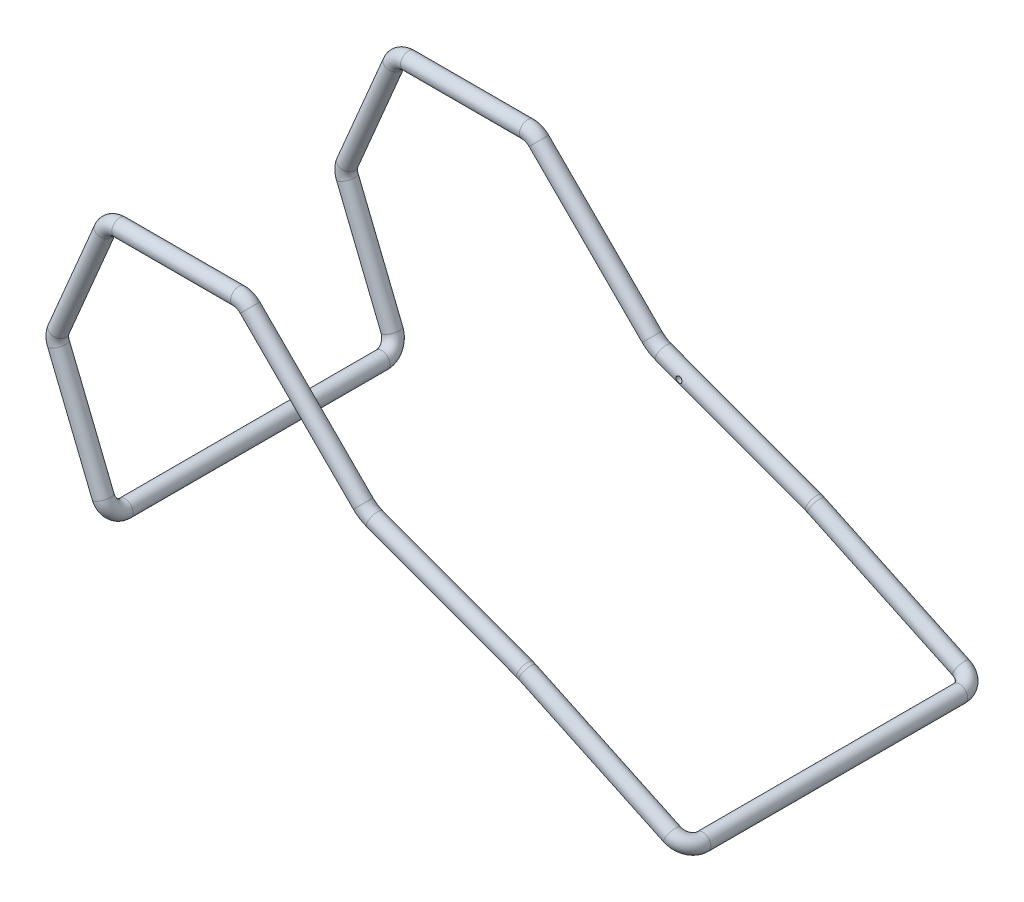
SolidWorks part; units mm, degrees
ref_plane "Front Plane" through (0, 0, 0) normal (0, 0, 1) x (1, 0, 0)
ref_plane "Top Plane" through (0, 0, 0) normal (0, 1, 0) x (1, 0, 0)
ref_plane "Right Plane" through (0, 0, 0) normal (1, 0, 0) x (0, 0, -1)
ref_plane "Plane1" through (0, 0, 304.8) normal (0, 0, 1) x (1, 0, 0)
ref_plane "Plane2" through (0, 0, -25.4) normal (0, 0, 1) x (1, 0, 0)
sketch3d "3DSketch1"
  line L0 (-9.5303, 23.5443, 0) -> (-80.1831, 198.0889, 0)
  line L1 (-80.0261, 217.5286, 0) -> (-6.5635, 390.9094, 0)
  line L2 (16.8238, 406.4, 0) -> (205.1258, 406.4, 0)
  line L3 (223.0863, 398.9605, 0) -> (402.1917, 219.8551, 0)
  line L4 (420.5449, 208.1105, 0) -> (658.2098, 120.5156, 0)
  line L5 (662.2973, 118.8031, 0) -> (891.4235, 10.8277, 0)
  line L6 (205.1258, 424.1672, 0) -> (205.1258, 377.3241, 0) construction
  line L8 (891.4235, 10.8277, -457.2) -> (662.2973, 118.8031, -457.2)
  line L11 (205.1258, 406.4, -457.2) -> (16.8238, 406.4, -457.2)
  line L12 (-6.5635, 390.9094, -457.2) -> (-80.0261, 217.5286, -457.2)
  line L13 (-80.1831, 198.0889, -457.2) -> (-9.5303, 23.5443, -457.2)
  line L15 (-6.5635, 390.9094, 0) -> (-6.5635, 390.9094, -457.2) construction
  line L16 (205.1258, 406.4, 0) -> (205.1258, 406.4, -457.2) construction
  line L17 (402.1917, 219.8551, 0) -> (402.1917, 219.8551, -457.2) construction
  line L18 (658.2098, 120.5156, 0) -> (658.2098, 120.5156, -457.2) construction
  line L19 (658.2098, 120.5156, -457.2) -> (420.5449, 208.1105, -457.2)
  line L20 (402.1917, 219.8551, -457.2) -> (223.0863, 398.9605, -457.2)
  line L21 (-6.5635, 390.9094, 0) -> (0, 406.4, 0) construction
  line L22 (0, 406.4, 0) -> (16.8238, 406.4, 0) construction
  line L23 (914.4, 0, -25.4) -> (914.4, 0, -431.8)
  line L24 (0, 0, -431.8) -> (0, 0, -25.4)
  line L25 (0, 0, -25.4) -> (0, 0, 0) construction
  line L26 (0, 0, -25.4) -> (914.4, 0, -25.4) construction
  line L27 (914.4, 0, -431.8) -> (0, 0, -431.8) construction
  arc A0 (-6.5635, 390.9094, 0) -> (16.8238, 406.4, 0) centre (16.8238, 381, 0) cw
  arc A1 (-80.0261, 217.5286, 0) -> (-80.1831, 198.0889, 0) centre (-56.6388, 207.6192, 0) cw
  arc A2 (205.1258, 406.4, 0) -> (223.0863, 398.9605, 0) centre (205.1258, 381, 0) cw
  arc A3 (402.1917, 219.8551, 0) -> (420.5449, 208.1105, 0) centre (438.1127, 255.7761, 0) cw
  arc A4 (658.2098, 120.5156, 0) -> (662.2973, 118.8031, 0) centre (640.642, 72.85, 0) cw
  arc A5 (891.4235, 10.8277, 0) -> (914.4, 0, -25.4) centre (891.4235, 10.8277, -25.4) ccw
  arc A6 (-80.0261, 217.5286, -457.2) -> (-80.1831, 198.0889, -457.2) centre (-56.6388, 207.6192, -457.2) ccw
  arc A7 (223.0863, 398.9605, -457.2) -> (205.1258, 406.4, -457.2) centre (205.1258, 381, -457.2) ccw
  arc A8 (16.8238, 406.4, -457.2) -> (-6.5635, 390.9094, -457.2) centre (16.8238, 381, -457.2) ccw
  arc A9 (662.2973, 118.8031, -457.2) -> (658.2098, 120.5156, -457.2) centre (640.642, 72.85, -457.2) ccw
  arc A10 (402.1917, 219.8551, -457.2) -> (420.5449, 208.1105, -457.2) centre (438.1127, 255.7761, -457.2) ccw
  arc A11 (914.4, 0, -431.8) -> (891.4235, 10.8277, -457.2) centre (891.4235, 10.8277, -431.8) ccw
  arc A12 (-9.5303, 23.5443, 0) -> (0, 0, -25.4) centre (-9.5303, 23.5443, -25.4) ccw
  arc A13 (-9.5303, 23.5443, -457.2) -> (0, 0, -431.8) centre (-9.5303, 23.5443, -431.8) ccw
  point P5 (892.403, 12.7, 0)
  point P7 (902.2511, 33.8042, -25.4)
  point P18 (16.8238, 381, -25.4)
  point P22 (-56.6388, 207.6192, 25.4)
  point P26 (205.1258, 381, -25.4)
  point P30 (438.1127, 255.7761, 50.8)
  point P34 (640.642, 72.85, -50.8)
  point P39 (-56.6388, 207.6192, -431.8)
  point P43 (0, 0, 0)
  point P44 (205.1258, 381, -431.8)
  point P48 (902.2511, 33.8042, -431.8)
  point P49 (16.8238, 381, -431.8)
  point P52 (660.2909, 119.7486, -457.2)
  point P53 (640.642, 72.85, -406.4)
  point P57 (438.1127, 255.7761, -406.4)
  point P59 (0, 0, 0)
  point P60 (14.0139, 33.0746, -25.4)
  point P64 (-33.0746, 14.0139, -431.8)
  point P65 (0, 0, 0)
  point P67 (469.8666, 237.3101, 0)
  point P68 (0, 0, 0)
  point P69 (0, 0, 0)
  dimension "D8" = 25.4
  dimension "D9" = 50.8
  dimension "D6" = 25.4
  dimension "D11" = 50.8
  dimension "D12" = 25.4
  dimension "D1" = 175
  dimension "D2" = 914.4
  dimension "D4" = 135
  dimension "D5" = 406.4
  dimension "D7" = 457.2
  dimension "D10" = 45
sketch "Sketch4" plane through (0, 0, -25.4) normal (0, 0, 1) x (1, 0, 0)
  circle A0 centre (0, 0) radius 12.7
  point P3 (0, 0)
  dimension "D1" = 25.4
sweep "Sweep3" add profiles "Sketch4" path "3DSketch1"
hole_wizard "3/8 (0.375) Diameter Hole1" positions "Sketch6" profile "Sketch7" hole size "3/8" standard "ANSI Inch"
sketch "Sketch6" plane through (0, 0, 0) normal (0, 0, 1) x (1, 0, 0)
  line L0 (452.808, 182.6843) -> (461.592, 206.5171) construction
  line L1 (416.1529, 196.1941) -> (653.8179, 108.5992) construction
  line L3 (662.6018, 132.432) -> (424.9368, 220.0269) construction
  point P0 (457.2, 194.6007)
  point P9 (0, 0)
  point P12 (463.8569, 190.8315)
  point P13 (463.4052, 190.1539)
  point P14 (457.2, 194.6007)
  dimension "D1" = 457.2
sketch "Sketch7" plane through (457.2, 194.6007, 0) normal (1, 0, 0) x (0, -1, 0)
  line L0 (0, 0) -> (0, 460.0616)
  line L1 (0, 460.0616) -> (4.7625, 457.2)
  line L2 (4.7625, 457.2) -> (4.7625, 0)
  line L5 (4.7625, 0) -> (0, 0)
  line L10 (0, 460.0616) -> (-4.7625, 457.2) construction
  line L11 (0, -6.35) -> (0, 107.95) construction
  dimension "Hole Dia." = 9.525
  dimension "Hole Depth" = 457.2
  dimension "Drill Angle" = 118
